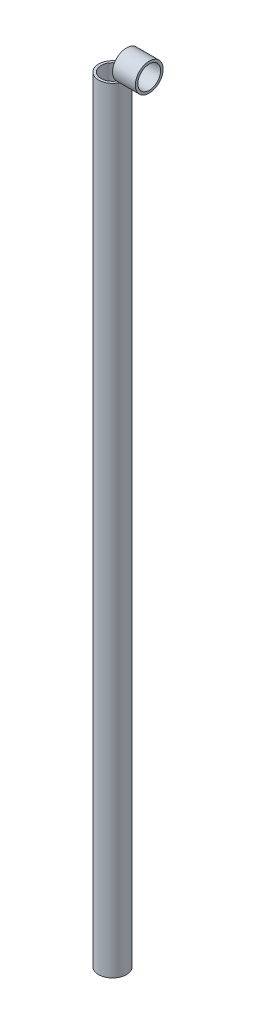
SolidWorks part; units mm, degrees
ref_plane "Front Plane" through (0, 0, 0) normal (0, 0, 1) x (1, 0, 0)
ref_plane "Top Plane" through (0, 0, 0) normal (0, 1, 0) x (1, 0, 0)
ref_plane "Right Plane" through (0, 0, 0) normal (1, 0, 0) x (0, 0, -1)
sketch "Sketch1" plane through (0, 0, 0) normal (0, 1, 0) x (1, 0, 0)
  circle A0 centre (0, 0) radius 17.4625
  circle A1 centre (0, 0) radius 14.2875
  dimension "D1" = 3.175
  dimension "D2" = 34.925
extrude "Boss-Extrude1" add sketch "Sketch1" along normal blind 971.55
sketch "Sketch2" plane through (0, 0, 0) normal (1, 0, 0) x (0, 0, -1)
  line L0 (17.4625, 971.55) -> (-17.4625, 971.55) construction
  circle A0 centre (0, 989.0125) radius 17.4625
  circle A1 centre (0, 989.0125) radius 14.2875
  dimension "D1" = 34.925
  dimension "D2" = 3.175
extrude "Boss-Extrude2" add sketch "Sketch2" along normal blind 28.575 from offset 17.4625
